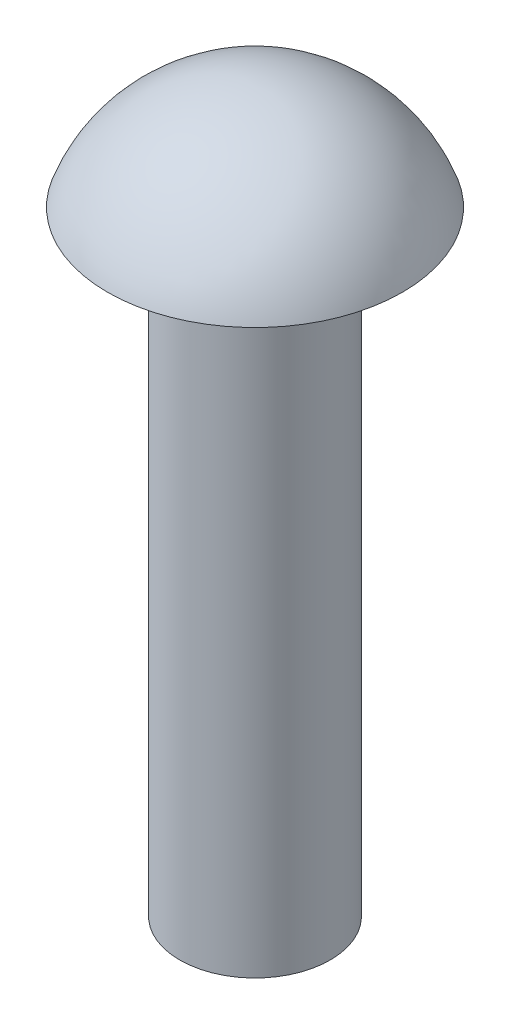
SolidWorks part; units mm, degrees
material "1060 Alloy"
ref_plane "Front Plane" through (0, 0, 0) normal (0, 0, 1) x (1, 0, 0)
ref_plane "Top Plane" through (0, 0, 0) normal (0, 1, 0) x (1, 0, 0)
ref_plane "Right Plane" through (0, 0, 0) normal (1, 0, 0) x (0, 0, -1)
sketch "Sketch1" plane through (0, 0, 0) normal (1, 0, 0) x (0, 0, -1)
  line L0 (0, 0) -> (0, -11.7) construction
  line L1 (0, -11.7) -> (1.225, -11.7)
  line L2 (1.225, -11.7) -> (1.225, -1.7)
  line L3 (1.225, -1.7) -> (2.4, -1.7)
  line L6 (0, 0) -> (0, -11.7)
  arc A0 (2.4, -1.7) -> (0, 0) centre (0, -2.5441) ccw
  point P7 (0, -2.0725)
  point P8 (0, -2.5332)
  point P12 (0, -0.8892)
  point P13 (10.6854, -6.8392)
  point P14 (0, -3.7896)
  point P15 (0, -3.491)
  point P16 (0, 0)
  point P18 (2.5965, -1.4)
  dimension "D4" = 2.4
  dimension "D1" = 2.45
  dimension "D2" = 10
  dimension "D3" = 1.7
revolve "Revolve2" add sketch "Sketch1" angle 360 about L0
